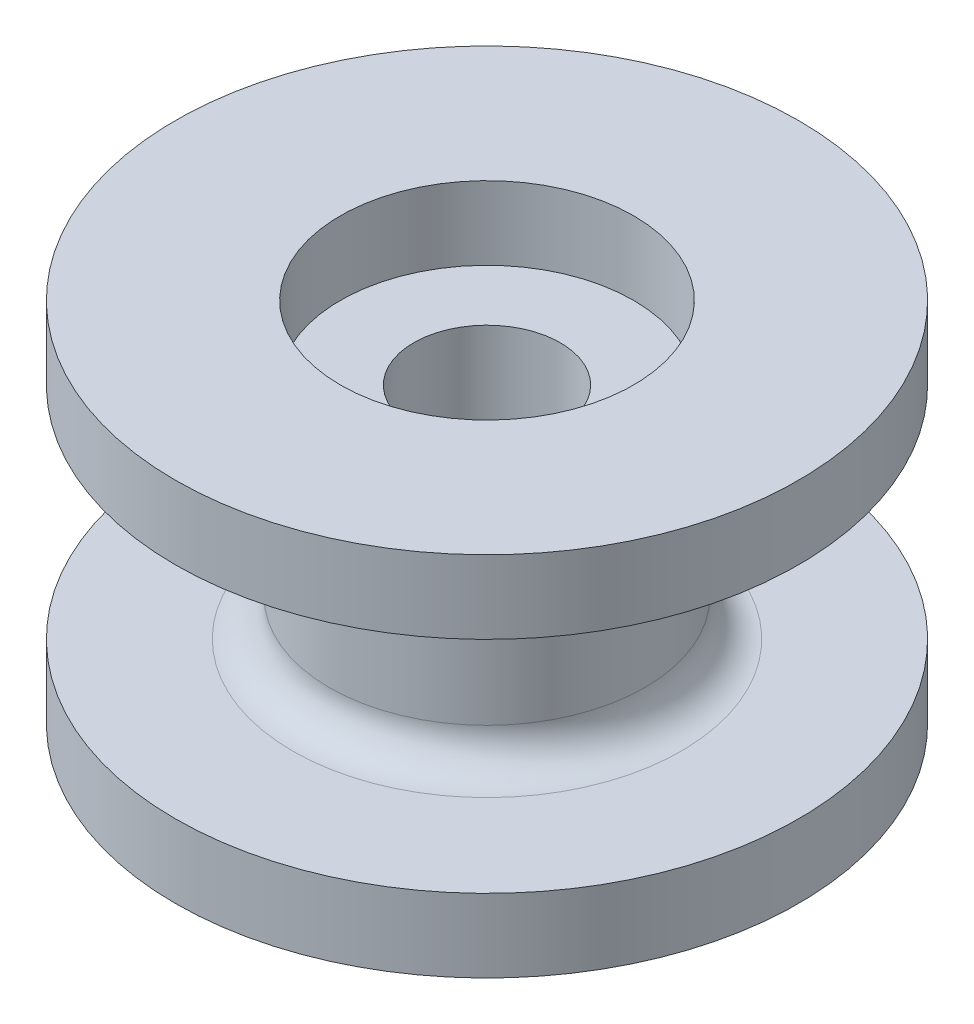
SolidWorks part; units mm, degrees
ref_plane "Front Plane" through (0, 0, 0) normal (0, 0, 1) x (1, 0, 0)
ref_plane "Top Plane" through (0, 0, 0) normal (0, 1, 0) x (1, 0, 0)
ref_plane "Right Plane" through (0, 0, 0) normal (1, 0, 0) x (0, 0, -1)
sketch "Sketch1" plane through (0, 0, 0) normal (0, 1, 0) x (1, 0, 0)
  circle A0 centre (0, 0) radius 8.5
  dimension "D1" = 17
extrude "Boss-Extrude1" add sketch "Sketch1" along normal blind 2
sketch "Sketch2" plane through (0, 2, 0) normal (0, 1, 0) x (1, 0, 0)
  circle A0 centre (0, 0) radius 4.3
  circle A1 centre (0, 0) radius 8.5 construction
  dimension "D1" = 4.2
extrude "Boss-Extrude2" add sketch "Sketch2" along normal blind 6
sketch "Sketch3" plane through (0, 8, 0) normal (0, 1, 0) x (1, 0, 0)
  circle A0 centre (0, 0) radius 8.5
  circle A2 centre (0, 0) radius 8.5 construction
  dimension "D1" = 0
extrude "Boss-Extrude3" add sketch "Sketch3" along normal blind 2
sketch "Sketch4" plane through (0, 10, 0) normal (0, 1, 0) x (1, 0, 0)
  circle A0 centre (0, 0) radius 4
extrude "Cut-Extrude1" cut sketch "Sketch4" against normal blind 2
sketch "Sketch5" plane through (0, 8, 0) normal (0, 1, 0) x (1, 0, 0)
  circle A0 centre (0, 0) radius 2
extrude "Cut-Extrude2" cut sketch "Sketch5" against normal blind 11
fillet "Fillet1" radius 1 2 edges at (0, 2, 4.3) (0, 8, 4.3)
